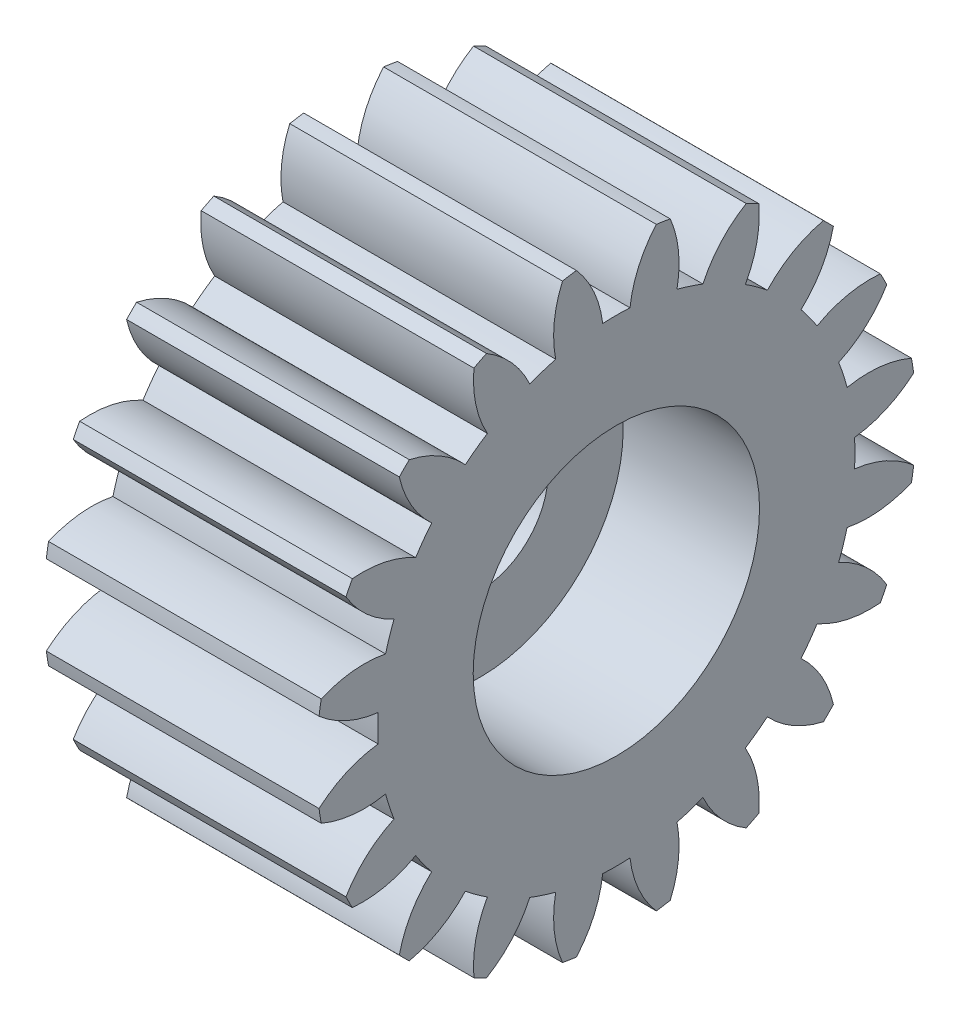
SolidWorks part; units mm, degrees
ref_plane "Plane1" through (0, 0, 0) normal (0, 0, 1) x (1, 0, 0)
ref_plane "Plane2" through (0, 0, 0) normal (0, 1, 0) x (1, 0, 0)
ref_plane "Plane3" through (0, 0, 0) normal (1, 0, 0) x (0, 0, -1)
sketch "HoldingSke" plane through (0, 0, 0) normal (0, 1, 0) x (1, 0, 0)
  line L0 (0, 0) -> (0.9397, -0.342)
  line L1 (-15, 0) -> (100, 0) construction
  line L2 (0, 0) -> (-2.1039, 2.3779)
  line L3 (0, 0) -> (-11.863, 4.5341)
  line L4 (0, 0) -> (8.1152, 2.9537)
  line L5 (0, 0) -> (-46.8476, -17.4728)
  line L6 (0, 0) -> (-8.2896, -5.593)
  line L7 (-2.1039, 2.3779) -> (8.6586, 51.2059)
  line L8 (-76.2, 54.61) -> (-76.1, 54.61)
  line L9 (-71.009, 38.7566) -> (-53.1078, 45.2721)
  line L10 (-76.2, 71.12) -> (104.1128, 71.12)
  line L11 (0, 0) -> (-10, 0)
  line L12 (-76.2, 101.6) -> (-76.162, 101.6)
  line L13 (24.9733, 27.94) -> (52.9518, 28.4284)
  line L14 (24.9733, 27.94) -> (24.9743, 27.94)
  line L15 (24.9733, 27.94) -> (100.4006, 29.5858)
  line L16 (-63.627, -1) -> (-12.827, -1)
  circle A0 centre (0, 0) radius 0.4
  circle A1 centre (0, 0) radius 8.749
  circle A2 centre (0, 0) radius 37.5
  circle A3 centre (0, 0) radius 0.4
  dimension "MHD" = 17.498
  dimension "Hub_dia" = 75
  dimension "Bore" = 0.8
  dimension "MBD" = 0.8
  dimension "Num_teeth" = 20
  dimension "Pitch" = 1
  dimension "Overall_len" = 50
  dimension "Show_teeth" = 20
  dimension "Thickness" = 10
  dimension "OAL" = 50.0001
  dimension "T_dim" = 0.1
  dimension "Ap" = 20
  dimension "H" = 19.05
  dimension "Pitch_radius" = 180.3128
  dimension "Width" = 10
  dimension "Backlash" = 0.038
  dimension "Addendum_fac" = 1
  dimension "Dedendum_fac" = 1.25
  dimension "Clearance_fac" = 0.25
  dimension "Dedendum_add" = 0.001
  dimension "Module" = 1
sketch "BasProSke" plane through (0, 0, 0) normal (0, 1, 0) x (1, 0, 0)
  line L0 (-10, 0) -> (60, 0) construction
  line L1 (0, 0) -> (0, 11)
  line L2 (0, 0) -> (10, 0)
  line L3 (10, 0) -> (10, 11)
  line L4 (10, 11) -> (0, 11)
  dimension "Thickness" = 10
  dimension "Diameter" = 22
revolve "Base-Revolve" add sketch "BasProSke" angle 360 about L0
sketch "TooCutSke" plane through (0, 0, 0) normal (1, 0, 0) x (0, 0, -1)
  line L1 (0, 0) -> (0, 107) construction
  line L2 (0, 0) -> (-0.8511, 9.9637) construction
  line L3 (0, 0) -> (-3.1206, 19.7028) construction
  line L4 (-0.8511, 9.9637) -> (-1.5603, 9.8514) construction
  arc A0 (0.4999, 8.7347) -> (-0.4999, 8.7347) centre (0, 0) ccw
  arc A1 (1.4852, 10.9249) -> (-1.4852, 10.9249) centre (0, 0) ccw
  circle A2 centre (0, 0) radius 10 construction
  circle A3 centre (0, 0) radius 9.3969 construction
  arc A4 (-0.4999, 8.7347) -> (-1.4852, 10.9249) centre (-4.4722, 8.2645) ccw
  arc A5 (1.4852, 10.9249) -> (0.4999, 8.7347) centre (4.4722, 8.2645) ccw
  dimension "Root_dia" = 17.498
  dimension "Overcut_dia" = 22.0508
  dimension "Pitch_dia" = 20
  dimension "Base_dia" = 18.7939
  dimension "Flank_rad" = 4
  dimension "Half_ang" = 9
  dimension "Half_CT" = 0.7181
extrude "ToothCut" cut sketch "TooCutSke" along normal through all
fillet "Breaks" [suppressed] radius 0.02
fillet "RootFillets" [suppressed] radius 0.251
pattern_circular "TeethCuts" count 20 every 18 about axis through (-10, 0, 0) along (1, 0, 0) of "ToothCut", "RootFillets", "Breaks"
sketch "HubNeaOneSke" plane through (0, 0, 0) normal (-1, 0, 0) x (0, 0, 1)
  circle A0 centre (0, 0) radius 8.749
  dimension "Diameter" = 17.498
extrude "HubNearOne" [suppressed] add sketch "HubNeaOneSke" along normal blind 40.0001
sketch "HubNeaBotSke" plane through (0, 0, 0) normal (-1, 0, 0) x (0, 0, 1)
  circle A0 centre (0, 0) radius 8.749
  dimension "Diameter" = 17.498
extrude "HubNearBoth" [suppressed] add sketch "HubNeaBotSke" along normal blind 20
ref_plane "FarPln" through (10, 0, 0) normal (1, 0, 0) x (0, 0, -1)
sketch "HubFarSke" plane through (10, 0, 0) normal (1, 0, 0) x (0, 0, -1)
  circle A0 centre (0, 0) radius 8.749
  dimension "Diameter" = 17.498
extrude "HubFar" [suppressed] add sketch "HubFarSke" along normal blind 20
sketch "BorSke" plane through (0, 0, 0) normal (1, 0, 0) x (0, 0, -1)
  circle A0 centre (0, 0) radius 0.4
  dimension "Diameter" = 0.8
extrude "Bore" cut sketch "BorSke" along normal mid plane 100.0001
sketch "KeySke" plane through (0, 0, 0) normal (1, 0, 0) x (0, 0, -1)
  line L0 (-0.05, 0) -> (-0.05, 0.5)
  line L1 (-0.05, 0.5) -> (0.05, 0.5)
  line L2 (0.05, 0.5) -> (0.05, 0)
  line L3 (0, 0) -> (0, 34) construction
  line L4 (-0.05, 0) -> (0.05, 0)
  dimension "Offset" = 0.5
  dimension "Width" = 0.1
extrude "Keyway" [suppressed] cut sketch "KeySke" along normal mid plane 100.0001
pattern_circular "Keyway2" [suppressed] count 2 every 90 about axis through (-10, 0, 0) along (1, 0, 0)
hole_wizard "Taladro de margen para M101" positions "Croquis1" profile "Croquis2" hole size "M10" standard "ISO" end condition through all
sketch "Croquis1" plane through (10, 0, 0) normal (1, 0, 0) x (0, 0, -1)
  point P0 (0, 0)
sketch "Croquis2" plane through (10, 0, 0) normal (0, 1, 0) x (0, 0, -1)
  line L0 (0, 0) -> (0, 10)
  line L1 (0, 10) -> (5.25, 10)
  line L2 (5.25, 10) -> (5.25, 0)
  line L5 (5.25, 0) -> (0, 0)
  line L11 (0, -6.35) -> (0, 107.95) construction
  dimension "Diámetro de taladro hasta el siguiente" = 10.5
  dimension "Profundidad de taladro hasta el siguiente" = 10
sketch "Croquis3" plane through (0, 0, 0) normal (-1, 0, 0) x (0, 0, 1)
  circle A0 centre (0, 0) radius 5.25
  circle A1 centre (0, 0) radius 2.5
  dimension "D1" = 5
extrude "Saliente-Extruir1" add sketch "Croquis3" against normal blind 5
equation "' \"Module@HoldingSke\" = 6.35"
equation "' \"Num_teeth@HoldingSke\" = 12"
equation "' \"Ap@HoldingSke\" =  20"
equation "' \"Ap@HoldingSke\" = 20"
equation "' \"Width@HoldingSke\" = 0.5 * 25.4"
equation "' \"Hub_dia@HoldingSke\"= 1 * 25.4"
equation "' \"Hub_dia@HoldingSke\" = 1 * 25.4"
equation "' \"Overall_len@HoldingSke\" = 1.0 * 25.4"
equation "' \"Bore@HoldingSke\" = 0.75 * 25.4"
equation "' \"T_dim@HoldingSke\" = 0.1 * 25.4"
equation "' \"Width@KeySke\" = 0.25 * 25.4"
equation "' \"Show_teeth@HoldingSke\" = 13"
equation "' \"Backlash@HoldingSke\" = 0.009 * 25.4"
equation "' \"Addendum_fac@HoldingSke\" = 1.0"
equation "' \"Dedendum_fac@HoldingSke\" = 1.25"
equation "' \"Dedendum_add@HoldingSke\" = 0.00005 * 25.4"
equation "' \"Clearance_fac@HoldingSke\" = 0.25"
equation "\"Pitch@HoldingSke\" = 1 / \"Module@HoldingSke\""
equation "\"Overcut_dia@TooCutSke\" = (\"Num_teeth@HoldingSke\" + 2 * \"Addendum_fac@HoldingSke\") / \"Pitch@HoldingSke\" + 0.002 * 25.4"
equation "\"Pitch_dia@TooCutSke\" = \"Num_teeth@HoldingSke\" / \"Pitch@HoldingSke\""
equation "\"Base_dia@TooCutSke\" = \"Num_teeth@HoldingSke\" / \"Pitch@HoldingSke\" * cos((\"Ap@HoldingSke\"  * 3.14159265 / 180))"
equation "\"Root_dia@TooCutSke\" = (\"Num_teeth@HoldingSke\" + 2) / \"Pitch@HoldingSke\" - 2 * (\"Addendum_fac@HoldingSke\" + \"Dedendum_fac@HoldingSke\") / \"Pitch@HoldingSke\" - \"Dedendum_add@HoldingSke\" * 2"
equation "\"Half_ang@TooCutSke\" = 180 / \"Num_teeth@HoldingSke\""
equation "\"Half_CT@TooCutSke\" = \"Num_teeth@HoldingSke\" / \"Pitch@HoldingSke\" * sin((3.14159265 / 2 / \"Num_teeth@HoldingSke\")) / 2 - 7 * \"Backlash@HoldingSke\" / 4"
equation "\"Flank_rad@TooCutSke\" = \"Num_teeth@HoldingSke\" / \"Pitch@HoldingSke\" / 5"
equation "\"Radius@RootFillets\" = \"Clearance_fac@HoldingSke\" / \"Pitch@HoldingSke\" + \"Dedendum_add@HoldingSke\""
equation "\"Break_rad@Breaks\" = 0.02 / \"Pitch@HoldingSke\""
equation "\"Thickness@HoldingSke\" = \"Width@HoldingSke\""
equation "\"OAL@HoldingSke\" = \"Thickness@HoldingSke\""
equation "\"MHD@HoldingSke\" = (\"Num_teeth@HoldingSke\" + 2) / \"Pitch@HoldingSke\" - 2 * (\"Addendum_fac@HoldingSke\" + \"Dedendum_fac@HoldingSke\")  / \"Pitch@HoldingSke\" - \"Dedendum_add@HoldingSke\" * 2"
equation "\"MBD@HoldingSke\" = (\"Num_teeth@HoldingSke\" + 2) / \"Pitch@HoldingSke\" - 2 * (\"Addendum_fac@HoldingSke\" + \"Dedendum_fac@HoldingSke\")  / \"Pitch@HoldingSke\" - \"Dedendum_add@HoldingSke\" * 2 - 0.002 * 25.4"
equation "\"MHD@HoldingSke\" = ((sgn( \"MHD@HoldingSke\" - \"Hub_dia@HoldingSke\" )-1)*( \"MHD@HoldingSke\" - \"Hub_dia@HoldingSke\" ))/-2+ \"Hub_dia@HoldingSke\""
equation "\"MBD@HoldingSke\" = ((sgn( \"MBD@HoldingSke\" - \"Bore@HoldingSke\" )-1)*( \"MBD@HoldingSke\" - \"Bore@HoldingSke\" ))/-2+ \"Bore@HoldingSke\""
equation "\"OAL@HoldingSke\" = ((sgn( \"OAL@HoldingSke\" - \"Overall_len@HoldingSke\" )+1)*( \"OAL@HoldingSke\" - \"Overall_len@HoldingSke\" ))/2 + \"Overall_len@HoldingSke\" + 0.000002 * 25.4"
equation "\"Num_teeth@TeethCuts\" = int( \"Show_teeth@HoldingSke\" ) + 1"
equation "\"Num_teeth@TeethCuts\" = ((sgn( \"Num_teeth@TeethCuts\" - \"Num_teeth@HoldingSke\" )-1)*( \"Num_teeth@TeethCuts\" - \"Num_teeth@HoldingSke\" ))/-2+ \"Num_teeth@HoldingSke\""
equation "\"Num_teeth@TeethCuts\" = ((sgn( \"Num_teeth@TeethCuts\" - 2.0)+1)*( \"Num_teeth@TeethCuts\" - 2.0))/2 +2.0"
equation "\"Angle@TeethCuts\" = 360.0 / \"Num_teeth@HoldingSke\""
equation "\"Diameter@BasProSke\" = (\"Num_teeth@HoldingSke\" + 2 * \"Addendum_fac@HoldingSke\") / \"Pitch@HoldingSke\""
equation "\"Thickness@BasProSke\"  = \"Thickness@HoldingSke\""
equation "' \"Fillet_rad@BasProSke\" =  \"Thickness@HoldingSke\" * 0.05"
equation "' \"Fillet_rad@BasProSke\" = \"Thickness@HoldingSke\" * 0.05"
equation "\"MHD@HoldingSke\" = ((sgn( \"MHD@HoldingSke\" - \"Root_dia@TooCutSke\" )-1)*( \"MHD@HoldingSke\" - \"Root_dia@TooCutSke\" ))/-2+ \"Root_dia@TooCutSke\""
equation "\"Diameter@HubNeaOneSke\" = \"MHD@HoldingSke\""
equation "\"Length@HubNearOne\" = \"OAL@HoldingSke\" - \"Thickness@BasProSke\""
equation "\"Diameter@HubNeaBotSke\" = \"MHD@HoldingSke\""
equation "\"Length@HubNearBoth\" = ( \"OAL@HoldingSke\" - \"Thickness@BasProSke\" ) / 2.0"
equation "\"Thickness@FarPln\" = \"Thickness@BasProSke\""
equation "\"Diameter@HubFarSke\" = \"MHD@HoldingSke\""
equation "\"Length@HubFar\" = ( \"OAL@HoldingSke\" - \"Thickness@BasProSke\" ) / 2.0"
equation "\"Diameter@BorSke\" = \"MBD@HoldingSke\""
equation "\"D1@Bore\" = \"OAL@HoldingSke\" * 2.0"
equation "\"D1@Keyway\" = \"OAL@HoldingSke\" * 2.0"
equation "\"Offset@KeySke\" = \"T_dim@HoldingSke\" + \"MBD@HoldingSke\" / 2.0"
